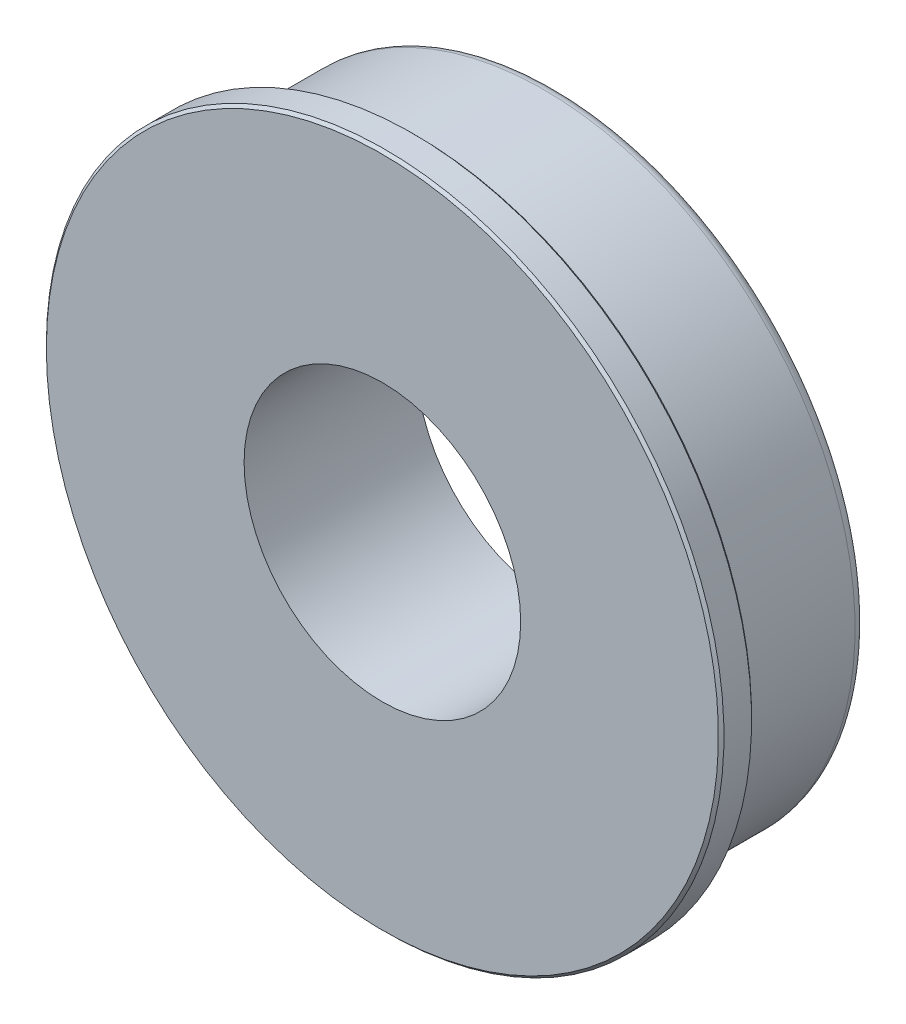
SolidWorks part; units mm, degrees
material "Plain Carbon Steel"
ref_plane "Front Plane" through (0, 0, 0) normal (0, 0, 1) x (1, 0, 0)
ref_plane "Top Plane" through (0, 0, 0) normal (0, 1, 0) x (1, 0, 0)
ref_plane "Right Plane" through (0, 0, 0) normal (1, 0, 0) x (0, 0, -1)
ref_plane "Plane1" through (0, 0, 0) normal (0, -1, 0) x (1, 0, 0)
sketch "Sketch1" plane through (0, 0, 0) normal (0, -1, 0) x (1, 0, 0)
  line L0 (14.2875, 0.508) -> (14.2875, 5.8953)
  line L1 (14.2875, 5.8953) -> (13.97, 5.8953)
  line L2 (13.97, 5.8953) -> (13.97, 6.4033)
  line L3 (13.97, 6.4033) -> (15.4305, 6.4033)
  line L4 (15.4305, 6.4033) -> (15.5575, 6.5303)
  line L5 (15.5575, 6.5303) -> (15.5575, 7.8003)
  line L6 (15.5575, 7.8003) -> (15.4305, 7.9273)
  line L7 (15.4305, 7.9273) -> (6.35, 7.9273)
  line L8 (6.35, 7.9273) -> (6.35, 0)
  line L9 (6.35, 0) -> (13.7795, 0)
  line L10 (0, 7.9273) -> (0, 0) construction
  arc A0 (13.7795, 0) -> (14.2875, 0.508) centre (13.7795, 0.508) ccw
revolve "Revolve1" add sketch "Sketch1" angle 360 about L10
